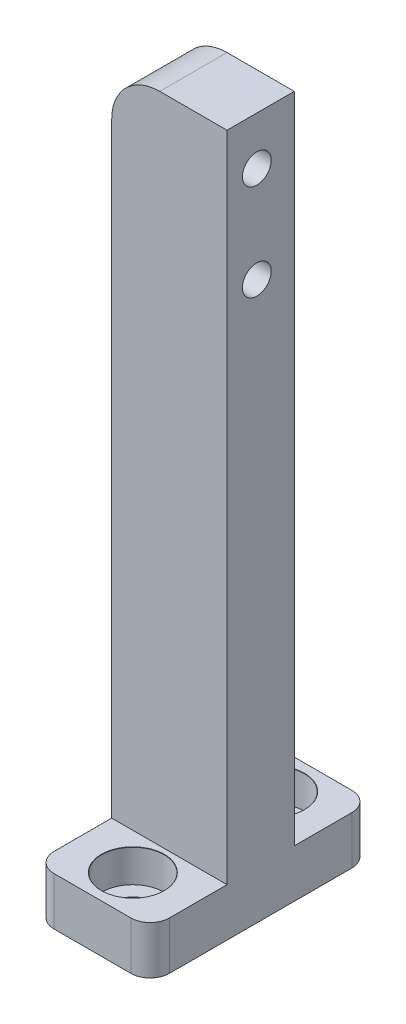
SolidWorks part; units mm, degrees
ref_plane "Front Plane" through (0, 0, 0) normal (0, 0, 1) x (1, 0, 0)
ref_plane "Top Plane" through (0, 0, 0) normal (0, 1, 0) x (1, 0, 0)
ref_plane "Right Plane" through (0, 0, 0) normal (1, 0, 0) x (0, 0, -1)
sketch "Sketch1" plane through (0, 0, 0) normal (0, 1, 0) x (1, 0, 0)
  line L1 (-6, -3.5) -> (6, -3.5)
  line L2 (-6, -3.5) -> (-6, 3.5)
  line L3 (-6, 3.5) -> (6, 3.5)
  line L4 (6, -3.5) -> (6, 3.5)
  line L5 (-6, -3.5) -> (6, 3.5) construction
  line L6 (-6, 3.5) -> (6, -3.5) construction
  point P0 (0, 0)
  dimension "D1" = 7
  dimension "D2" = 12
extrude "Boss-Extrude1" add sketch "Sketch1" along normal mid plane 73
sketch "Sketch3" plane through (0, 0, 0) normal (0, 0, 1) x (1, 0, 0)
  line L0 (-6, 36.5) -> (-6, -36.5) construction
  line L1 (-6, -31.5) -> (6, -31.5)
  line L2 (-6, -31.5) -> (-6, -36.5)
  line L3 (-6, -36.5) -> (6, -36.5)
  line L4 (6, -31.5) -> (6, -36.5)
  dimension "D1" = 5
extrude "Boss-Extrude2" add sketch "Sketch3" along normal mid plane 23
fillet "Fillet1" radius 2 4 edges at (-6, -34, -11.5) (6, -34, -11.5) (-6, -34, 11.5) (6, -34, 11.5)
hole_wizard "CBORE for M3 Hex Socket Head Cap Screw1" positions "Sketch4" profile "Sketch6" counterbore size "M3" standard "DIN" end condition through all
sketch "Sketch4" plane through (0, -31.5, 0) normal (0, 1, 0) x (1, 0, 0)
  line L0 (6, 3.5) -> (-6, 3.5) construction
  point P0 (0, 7.3)
  dimension "D1" = 3.8
sketch "Sketch6" plane through (0, -31.5, -7.3) normal (1, 0, 0) x (0, 0, 1)
  line L0 (0, 0) -> (0, 5)
  line L1 (0, 5) -> (1.7, 5)
  line L3 (1.7, 5) -> (1.7, 3.4)
  line L4 (3.25, 3.4) -> (1.7, 3.4)
  line L5 (3.25, 3.4) -> (3.25, 0.025)
  line L6 (3.25, 0.025) -> (3.275, 0)
  line L7 (3.275, 0) -> (0, 0)
  line L8 (-3.25, 0.025) -> (-3.275, 0) construction
  line L11 (0, -6.35) -> (0, 107.95) construction
  dimension "Thru Hole Dia." = 3.4
  dimension "Thru Hole Depth" = 5
  dimension "C'Bore Dia." = 6.5
  dimension "C'Bore Depth" = 3.4
  dimension "Near C'Sink Dia." = 6.55
  dimension "Near C'Sink Angle" = 90
mirror "Mirror1" about plane through (0, 0, 0) normal (0, 0, 1) of "CBORE for M3 Hex Socket Head Cap Screw1"
fillet "Fillet2" radius 5 1 edges at (-6, 36.5, 0)
sketch "Sketch7" plane through (6, 0, 0) normal (1, 0, 0) x (0, 0, -1)
  line L0 (-3.5, 36.5) -> (3.5, 36.5) construction
  line L1 (-3.5, 36.5) -> (-3.5, -31.5) construction
  circle A0 centre (-0.4, 31.5) radius 1.5
  circle A1 centre (-0.4, 21.5) radius 1.5
  dimension "D1" = 3
  dimension "D2" = 5
  dimension "D3" = 10
  dimension "D4" = 3.1
extrude "Cut-Extrude1" cut sketch "Sketch7" against normal up to next
